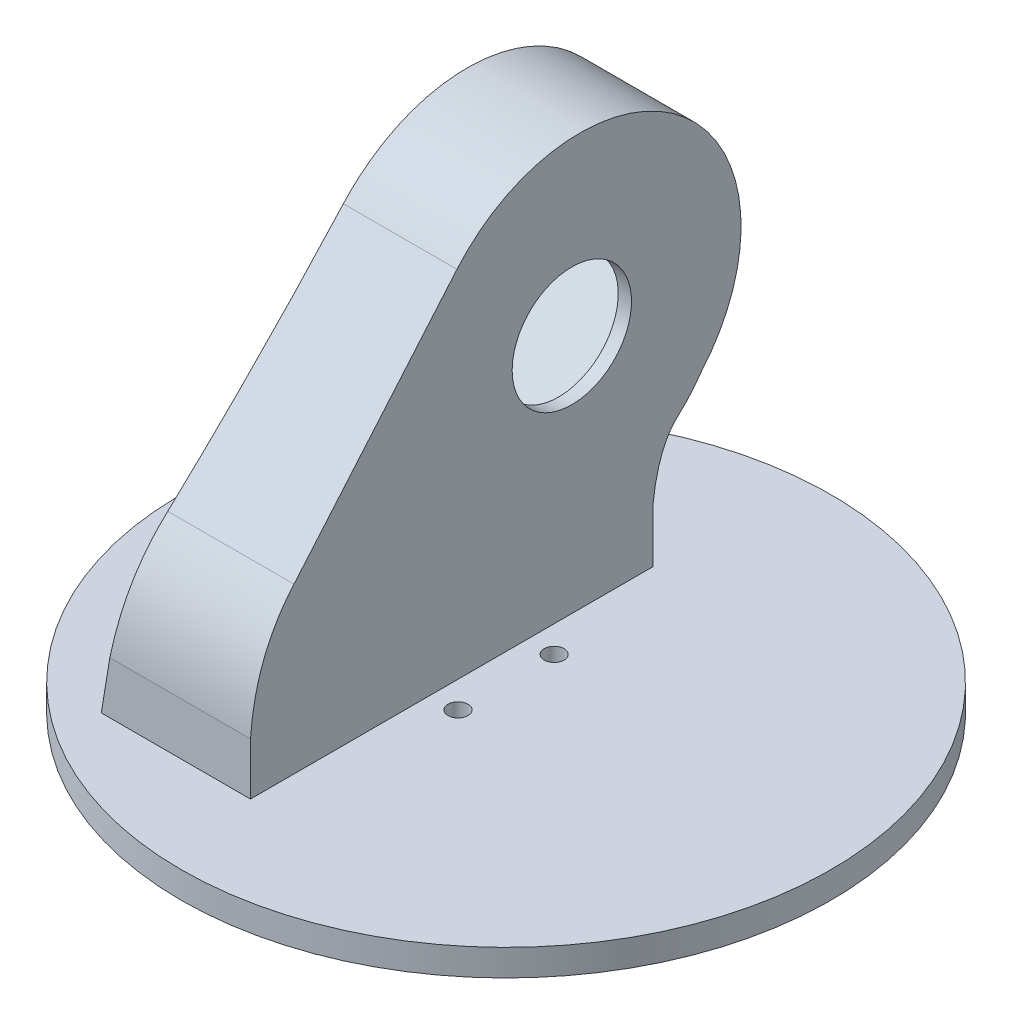
SolidWorks part; units mm, degrees
ref_plane "Alzado" through (0, 0, 0) normal (0, 0, 1) x (1, 0, 0)
ref_plane "Planta" through (0, 0, 0) normal (0, 1, 0) x (1, 0, 0)
ref_plane "Vista lateral" through (0, 0, 0) normal (1, 0, 0) x (0, 0, -1)
sketch "Croquis1" plane through (0, 0, 0) normal (0, 1, 0) x (1, 0, 0)
  circle A0 centre (0, 0) radius 49
  dimension "D1" = 98
extrude "Saliente-Extruir1" add sketch "Croquis1" along normal blind 4
sketch "Croquis2" plane through (0, 4, 0) normal (0, 1, 0) x (1, 0, 0)
  circle A0 centre (0, 7.25) radius 1.5
  circle A1 centre (0, -7.25) radius 1.5
  dimension "D1" = 3
  dimension "D2" = 3
  dimension "D3" = 7.25
  dimension "D4" = 7.25
extrude "Cortar-Extruir1" cut sketch "Croquis2" against normal blind 4
sketch "Croquis3" plane through (0, 4, 0) normal (0, 1, 0) x (1, 0, 0)
  line L0 (-4, 26.129) -> (-4, -34.55)
  line L1 (-4, -34.55) -> (-26.5, -34.55)
  line L2 (-26.5, -34.55) -> (-26.5, 26.129)
  line L3 (-26.5, 26.129) -> (-4, 26.129)
  dimension "D1" = 60.679
  dimension "D2" = 22.5
  dimension "D3" = 26.5
  dimension "D4" = 26.129
extrude "Saliente-Extruir2" add sketch "Croquis3" along normal blind 60.773
sketch "Croquis4" plane through (-4, 0, 0) normal (1, 0, 0) x (0, 0, -1)
  line L0 (-34.55, 4) -> (-34.55, 11.858)
  line L1 (-34.55, 64.773) -> (-34.55, 4) construction
  line L3 (26.129, 64.773) -> (26.129, 4) construction
  line L4 (26.129, 11.858) -> (26.129, 4)
  line L8 (-28.575, 28.098) -> (-3.407, 57.621)
  line L11 (-34.55, 4) -> (26.129, 4)
  arc A0 (-3.407, 57.621) -> (33.465, 25.858) centre (15.111, 41.8347) cw
  spline S0 degree 2 poles (26.129, 11.858) (26.8492, 18.8575) (29.748, 21.629) knots 0 0 0 0.117773 0.117773 0.117773
  spline S1 degree 2 poles (29.748, 21.629) (31.899, 23.5432) (33.465, 25.858) knots 0 0 0 0.522922 0.522922 0.522922
  spline S2 degree 2 poles (-34.55, 11.858) (-34.0266, 21.5143) (-28.575, 28.098) knots 0 0 0 0.824436 0.824436 0.824436
  point P11 (0, 0)
  dimension "D1" = 7.858
extrude "Saliente-Extruir3" add sketch "Croquis4" against normal blind 22.5
sketch "Croquis5" plane through (-4, 0, 0) normal (1, 0, 0) x (0, 0, -1)
  line L0 (-3.407, 57.621) -> (-28.575, 28.098)
  line L1 (6.9896, 64.773) -> (-34.55, 64.773)
  line L2 (-34.55, 64.773) -> (-34.55, 11.858)
  line L3 (23.2323, 64.773) -> (26.129, 64.773)
  line L4 (26.129, 64.773) -> (26.129, 63.5309)
  arc A0 (-3.407, 57.621) -> (6.9896, 64.773) centre (15.111, 41.8347) cw
  arc A1 (23.2323, 64.773) -> (26.129, 63.5309) centre (15.111, 41.8347) cw
  spline S0 degree 3 poles (-34.55, 11.858) (-34.0704, 18.7421) (-31.8821, 24.3861) (-27.9851, 28.79) knots 0 0 0 0 0.63862 0.63862 0.63862 0.63862
  point P0 (6.9896, 64.773)
  point P1 (-34.55, 11.858)
  point P3 (-3.407, 57.621)
  point P5 (-28.575, 28.098)
  point P7 (23.2323, 64.773)
  point P9 (26.129, 64.773)
  point P11 (26.129, 63.5309)
  line M1 (-34.55, 64.773) -> (-34.55, 4)
  line M7 (26.129, 63.5309) -> (26.129, 64.773)
  line M8 (26.129, 64.773) -> (23.2323, 64.773)
  line M10 (6.9896, 64.773) -> (-34.55, 64.773)
extrude "Cortar-Extruir2" cut sketch "Croquis5" against normal blind 22.5 contours S0 L0 A0 M1 M10 | A1 M8 M7
sketch "Croquis9" plane through (-26.5, 0, 0) normal (-1, 0, 0) x (0, 0, 1)
  line L0 (25.55, 4) -> (25.55, 7.838)
  line L1 (-26.129, 4) -> (34.55, 4) construction
  line L12 (-15.129, 4) -> (25.55, 4)
  line L14 (1.124, 55.6748) -> (11.753, 43.195)
  arc A0 (-31.1921, 27.816) -> (1.124, 55.6748) centre (-15.034, 41.7454) cw
  spline S0 degree 2 poles (-15.129, 4) (-20.706, 17.6292) (-31.1921, 27.816) knots 0 0 0 1 1 1
  spline S1 degree 2 poles (25.55, 7.838) (24.8863, 23.9569) (17.259, 35.7) knots 0 0 0 0.526933 0.526933 0.526933
  spline S2 degree 2 poles (17.259, 35.7) (14.8342, 39.7503) (11.753, 43.195) knots 0 0 0 0.431109 0.431109 0.431109
  dimension "D6" = 29.4265
extrude "Cortar-Extruir5" cut sketch "Croquis9" against normal blind 8.5
sketch "Croquis10" plane through (0, 0, -26.129) normal (0, 0, -1) x (-1, 0, 0)
  line L1 (26.5, 66.1683) -> (4, 66.1683) construction
  line L2 (21, 66.1683) -> (26.5, 66.1683)
  line L3 (26.5, 66.1683) -> (26.5, 4)
  spline S0 degree 2 poles (21, 66.1683) (21.1409, 34.6708) (26.5, 4) knots 0 0 0 0.615166 0.615166 0.615166
extrude "Cortar-Extruir6" cut sketch "Croquis10" against normal blind 78.5 and the other way blind 29.5
sketch "Croquis11" plane through (-18, 0, 0) normal (-1, 0, 0) x (0, 0, 1)
  line L0 (-15.129, 4) -> (25.55, 4) construction
  line L1 (0.401, 11.108) -> (15.25, 25.957)
  line L3 (-13.741, 54.948) -> (-28.59, 40.099)
  line L4 (-28.59, 40.099) -> (0.401, 11.108)
  line L5 (-13.741, 54.948) -> (15.25, 25.957)
  point P0 (0.401, 11.108)
  point P4 (15.25, 25.957)
  point P9 (-28.59, 40.099)
  point P10 (-13.741, 54.948)
  dimension "D1" = 15.53
  dimension "D2" = 7.108
  dimension "D3" = 21.957
  dimension "D4" = 10.3
  dimension "D5" = 13.461
  dimension "D6" = 36.099
  dimension "D7" = 40.9995
  dimension "D8" = 20.9997
extrude "Cortar-Extruir7" cut sketch "Croquis11" against normal blind 12
sketch "Croquis12" plane through (-6, 0, 0) normal (-1, 0, 0) x (0, 0, 1)
  circle A0 centre (-13.918, 40.276) radius 9
  dimension "D1" = 18
  dimension "D2" = 14.672
  dimension "D3" = 14.672
extrude "Cortar-Extruir8" cut sketch "Croquis12" against normal up to next
sketch "Croquis13" plane through (-18, 0, 0) normal (-1, 0, 0) x (0, 0, 1)
  line L0 (15.25, 25.957) -> (-13.741, 54.948) construction
  line L1 (-28.59, 40.099) -> (0.401, 11.108) construction
  line L2 (-28.59, 40.099) -> (0.401, 11.108) construction
  line L3 (15.25, 25.957) -> (-13.741, 54.948) construction
  circle A0 centre (-27.1768, 46.464) radius 1.3
  circle A1 centre (-20.1047, 53.5335) radius 1.3
  circle A2 centre (6.766, 12.5212) radius 1.3
  circle A3 centre (13.8368, 19.592) radius 1.3
  point P20 (15.25, 25.957)
  dimension "D1" = 2.6
  dimension "D2" = 6.519
  dimension "D3" = 5.5
  dimension "D4" = 6.52
  dimension "D5" = 5.5
  dimension "D6" = 6.52
  dimension "D7" = 5.5
  dimension "D8" = 6.52
  dimension "D9" = 5.5
extrude "Cortar-Extruir9" cut sketch "Croquis13" against normal blind 5
sketch "Croquis14" plane through (0, 0, 0) normal (0, -1, 0) x (1, 0, 0)
  circle A0 centre (0, 0) radius 3.75
  dimension "D1" = 7.5
extrude "Cortar-Extruir10" cut sketch "Croquis14" against normal blind 2
